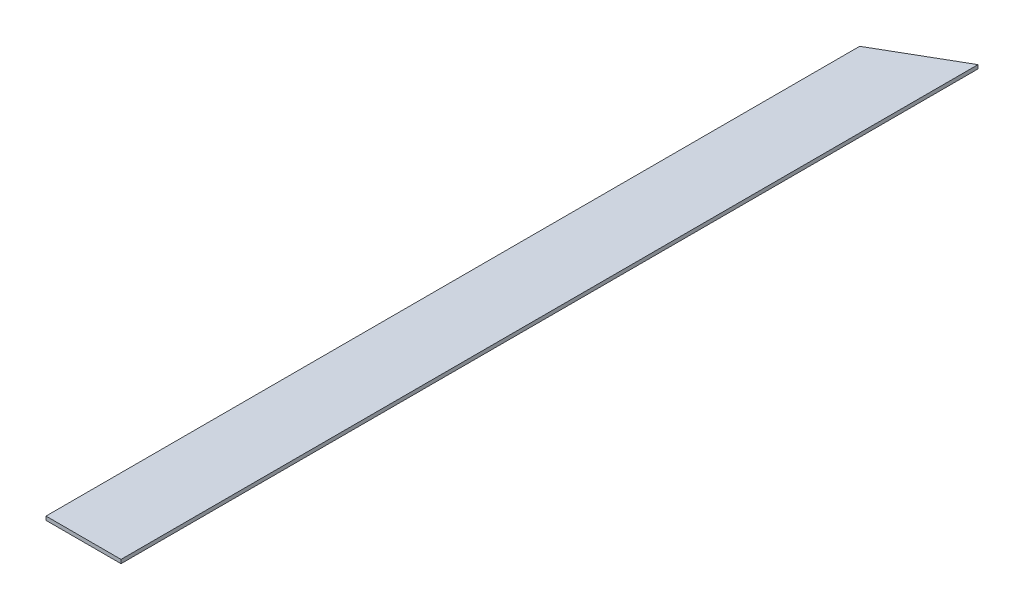
SolidWorks part; units mm, degrees
ref_plane "Front Plane" through (0, 0, 0) normal (0, 0, 1) x (1, 0, 0)
ref_plane "Top Plane" through (0, 0, 0) normal (0, 1, 0) x (1, 0, 0)
ref_plane "Right Plane" through (0, 0, 0) normal (1, 0, 0) x (0, 0, -1)
sketch "Sketch1" plane through (0, 0, 0) normal (0, 1, 0) x (1, 0, 0)
  line L0 (-25.4, 0) -> (25.4, 0)
  line L1 (25.4, 0) -> (25.4, 580.136)
  line L2 (25.4, 580.136) -> (-25.4, 550.8302)
  line L3 (-25.4, 550.8302) -> (-25.4, 0)
  dimension "D1" = 50.8
  dimension "D2" = 25.4
  dimension "D3" = 580.136
  dimension "D4" = 240.02
extrude "Boss-Extrude1" add sketch "Sketch1" along normal blind 2.54
